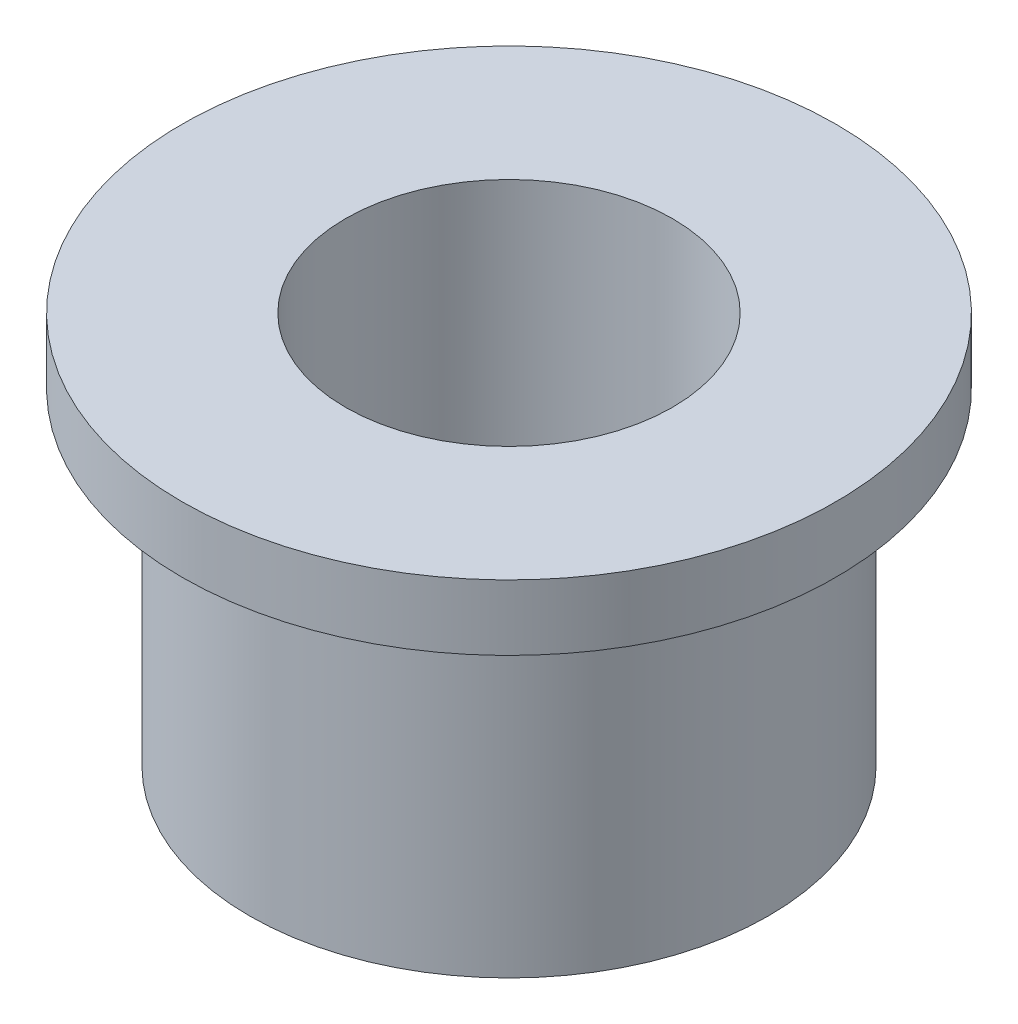
SolidWorks part; units mm, degrees
material "Delrin 2700 NC010, Low Viscosity Acetal Copolymer (SS)"
ref_plane "Front Plane" through (0, 0, 0) normal (0, 0, 1) x (1, 0, 0)
ref_plane "Top Plane" through (0, 0, 0) normal (0, 1, 0) x (1, 0, 0)
ref_plane "Right Plane" through (0, 0, 0) normal (1, 0, 0) x (0, 0, -1)
sketch "Sketch1" plane through (0, 0, 0) normal (0, 0, 1) x (1, 0, 0)
  line L0 (0, 0) -> (0, -10.9677) construction
  line L1 (5, 1.0323) -> (5, -10.9677)
  line L2 (5, -10.9677) -> (7.9375, -10.9677)
  line L3 (7.9375, -10.9677) -> (7.9375, -0.9677)
  line L4 (7.9375, -0.9677) -> (10, -0.9677)
  line L5 (10, -0.9677) -> (10, 1.0323)
  line L6 (10, 1.0323) -> (5, 1.0323)
  dimension "D1" = 2
  dimension "D2" = 10
  dimension "D3" = 5
  dimension "D4" = 7.9375
  dimension "D5" = 10
revolve "Revolve1" add sketch "Sketch1" angle 360 about L0
equation "\"D4@Sketch1\"=7.9375"
